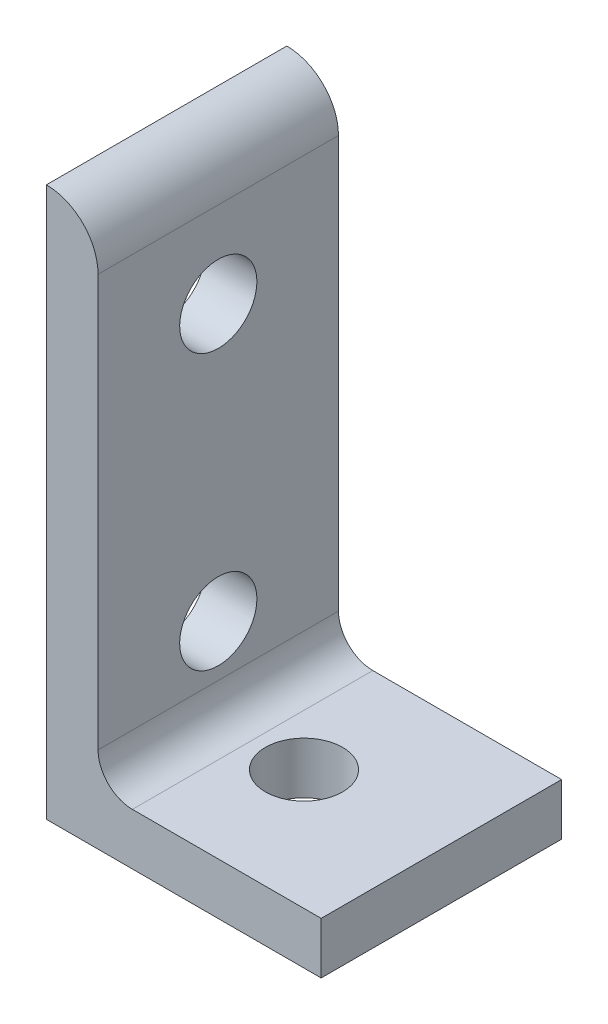
SolidWorks part; units mm, degrees
material "6061-T6 (SS)"
ref_plane "Front Plane" through (0, 0, 0) normal (0, 0, 1) x (1, 0, 0)
ref_plane "Top Plane" through (0, 0, 0) normal (0, 1, 0) x (1, 0, 0)
ref_plane "Right Plane" through (0, 0, 0) normal (1, 0, 0) x (0, 0, -1)
sketch "Sketch1" plane through (0, 0, 0) normal (0, 0, 1) x (1, 0, 0)
  line L0 (0, 0) -> (0, 50.8)
  line L1 (4.7752, 46.0248) -> (4.7752, 50.8) construction
  line L2 (4.7752, 46.0248) -> (4.7752, 7.9502)
  line L3 (7.9502, 4.7752) -> (46.0248, 4.7752)
  line L4 (4.7752, 50.8) -> (0, 50.8) construction
  line L5 (50.8, 0) -> (0, 0)
  line L6 (46.0248, 4.7752) -> (50.8, 4.7752) construction
  line L7 (50.8, 4.7752) -> (50.8, 0) construction
  arc A0 (4.7752, 46.0248) -> (0, 50.8) centre (0, 46.0248) ccw
  arc A1 (50.8, 0) -> (46.0248, 4.7752) centre (46.0248, 0) ccw
  arc A2 (4.7752, 7.9502) -> (7.9502, 4.7752) centre (7.9502, 7.9502) ccw
  point P10 (4.7752, 48.4124)
  dimension "E" = 3.175
  dimension "D" = 4.7752
  dimension "C" = 50.8
  dimension "B" = 50.8
extrude "Boss-Extrude1" add sketch "Sketch1" along normal mid plane 22.225
sketch "Sketch2" plane through (0, 0, 0) normal (0, 1, 0) x (1, 0, 0)
  line L0 (0, 0) -> (12.7, 0) construction
  line L1 (12.7, 0) -> (38.1, 0) construction
  circle A0 centre (12.7, 0) radius 3.5687
  circle A1 centre (38.1, 0) radius 3.5687
extrude "Cut-Extrude1" cut sketch "Sketch2" along normal through all
sketch "Sketch3" plane through (0, 0, 0) normal (1, 0, 0) x (0, 0, -1)
  line L0 (0, 0) -> (0, 12.7) construction
  line L1 (0, 12.7) -> (0, 38.1) construction
  circle A0 centre (0, 12.7) radius 3.5687
  circle A1 centre (0, 38.1) radius 3.5687
  dimension "D1" = 12.7
  dimension "D2" = 25.4
extrude "Cut-Extrude2" cut sketch "Sketch3" along normal through all
sketch "Sketch4" plane through (0, 4.7752, 0) normal (0, 1, 0) x (1, 0, 0)
  line L0 (46.0248, -11.1125) -> (7.9502, -11.1125) construction
  line L1 (50.8, 11.1125) -> (25.4, 11.1125)
  line L2 (50.8, 11.1125) -> (50.8, -11.1125)
  line L3 (50.8, -11.1125) -> (25.4, -11.1125)
  line L4 (25.4, 11.1125) -> (25.4, -11.1125)
  line L5 (25.4, 11.1125) -> (0, 11.1125) construction
  point P8 (0, 0)
extrude "Cut-Extrude3" cut sketch "Sketch4" against normal up to next
equation "\"E@Sketch3\" = \"E@Sketch2\""
equation "\"D1@Sketch3\" = \"D1@Sketch2\""
equation "\"D2@Sketch3\" = \"D2@Sketch2\""
